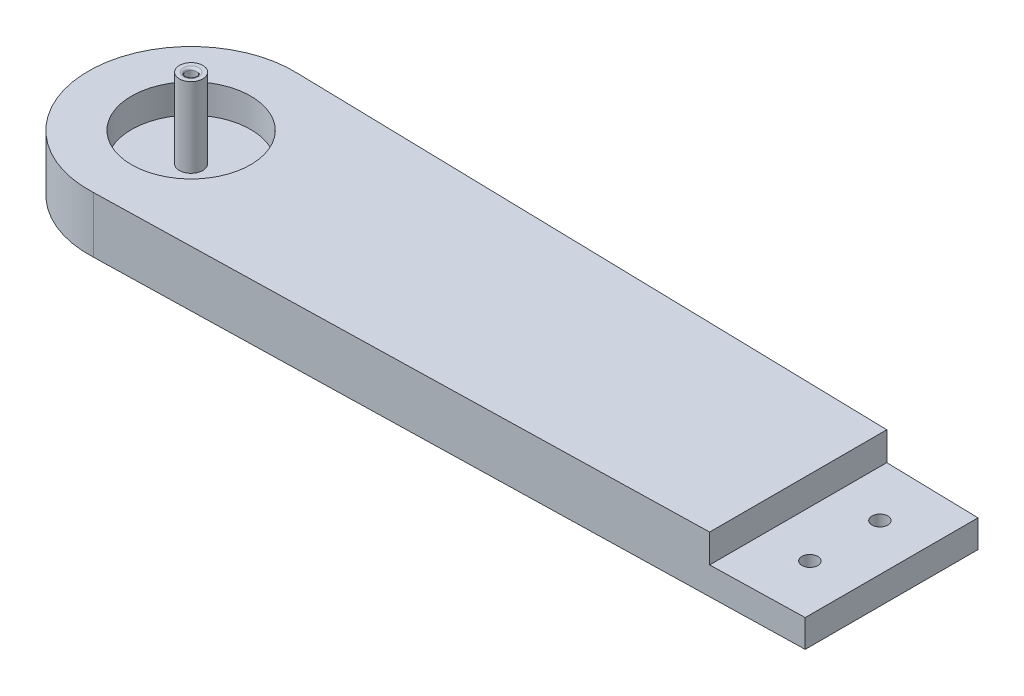
SolidWorks part; units mm, degrees
ref_plane "Front Plane" through (0, 0, 0) normal (0, 0, 1) x (1, 0, 0)
ref_plane "Top Plane" through (0, 0, 0) normal (0, 1, 0) x (1, 0, 0)
ref_plane "Right Plane" through (0, 0, 0) normal (1, 0, 0) x (0, 0, -1)
sketch "Sketch1" plane through (0, 0, 0) normal (0, 1, 0) x (1, 0, 0)
  circle A0 centre (0, 0) radius 22
  dimension "D1" = 44
extrude "Boss-Extrude1" add sketch "Sketch1" along normal blind 12
sketch "Sketch2" plane through (0, 12, 0) normal (0, 1, 0) x (1, 0, 0)
  circle A0 centre (0, 0) radius 12.75
  dimension "D1" = 25.5
extrude "Cut-Extrude1" cut sketch "Sketch2" against normal blind 6.2
sketch "Sketch5" plane through (0, 5.8, 0) normal (0, 1, 0) x (1, 0, 0)
  circle A0 centre (0, 0) radius 2.5
  dimension "D1" = 5
extrude "Boss-Extrude2" add sketch "Sketch5" along normal blind 17
sketch "Sketch6" plane through (0, 0, 0) normal (0, -1, 0) x (1, 0, 0)
  circle A0 centre (0, 0) radius 1.15
  dimension "D1" = 2.3
extrude "Cut-Extrude2" cut sketch "Sketch6" against normal blind 34.1
sketch "Sketch7" plane through (0, 0, 0) normal (0, -1, 0) x (1, 0, 0)
  circle A0 centre (0, 0) radius 2
  dimension "D1" = 4
extrude "Cut-Extrude3" cut sketch "Sketch7" against normal blind 20
fillet "Fillet1" radius 1 1 edges at (0, 0, -2)
fillet "Fillet2" radius 0.5 1 edges at (0, 22.8, 1.15)
sketch "Sketch8" plane through (0, 0, 0) normal (0, -1, 0) x (1, 0, 0)
  line L0 (0, 0) -> (150, 0) construction
  line L1 (150, 18.5) -> (0, 22)
  line L2 (0, -22) -> (150, -18.5)
  line L3 (150, 18.5) -> (150, -18.5)
  line L4 (0, 22) -> (0, -22)
  circle A0 centre (150, 0) radius 18.5
  circle A1 centre (0, 0) radius 22 construction
  circle A3 centre (0, 0) radius 22
  circle A4 centre (0, 0) radius 22
  circle M5 centre (0, 0) radius 22
  dimension "D1" = 0
  dimension "D2" = 37
  dimension "D3" = 150
extrude "Boss-Extrude4" add sketch "Sketch8" against normal blind 12 contours L0 L2 A0 M5 | A4 L0 A0 L1 | A0 L0 L3 | L0 A0 L3
sketch "Sketch9" plane through (0, 12, 0) normal (0, 1, 0) x (1, 0, 0)
  line L0 (150, 0) -> (130, 0) construction
  line L1 (150, -18.5) -> (150, 18.5) construction
  line L2 (130, 18.9667) -> (130, -18.9667)
  line L3 (150, -18.5) -> (1.0261, -21.9761) construction
  line L7 (1.0261, -21.9761) -> (150, -18.5)
  line L8 (150, -18.5) -> (150, 18.5)
  line L9 (150, 18.5) -> (1.0261, 21.9761)
  line L10 (1.0261, -21.9761) -> (150, -18.5)
  line L11 (150, -18.5) -> (150, 18.5)
  line L12 (150, 18.5) -> (1.0261, 21.9761)
  arc A1 (1.0261, 21.9761) -> (1.0261, -21.9761) centre (0, 0) ccw
  arc A2 (1.0261, 21.9761) -> (1.0261, -21.9761) centre (0, 0) ccw
  point P10 (130, 0)
  dimension "D1" = 0
extrude "Cut-Extrude5" cut sketch "Sketch9" against normal blind 6.1 contours L0 L11 L7 L2 | L3 L0 L2
sketch "Sketch10" plane through (0, 0, 0) normal (0, -1, 0) x (1, 0, 0)
  line L0 (150, 0) -> (140, 0) construction
  line L1 (150, 18.5) -> (150, -18.5) construction
  line L2 (140, 7.5) -> (140, -7.5) construction
  circle A0 centre (140, 7.5) radius 1.7
  circle A1 centre (140, -7.5) radius 1.7
  point P8 (140, 0)
  dimension "D1" = 10
  dimension "D2" = 15
extrude "Cut-Extrude6" cut sketch "Sketch10" against normal blind 6.1 contours A1 | A0
sketch "Sketch11" plane through (0, 0, 0) normal (0, -1, 0) x (1, 0, 0)
  circle A0 centre (140, 7.5) radius 2.8
  circle A1 centre (140, -7.5) radius 2.8
extrude "Cut-Extrude7" cut sketch "Sketch11" against normal blind 3
fillet "Fillet3" radius 0.5 2 edges at (140, 0, -10.3) (140, 0, 4.7)
